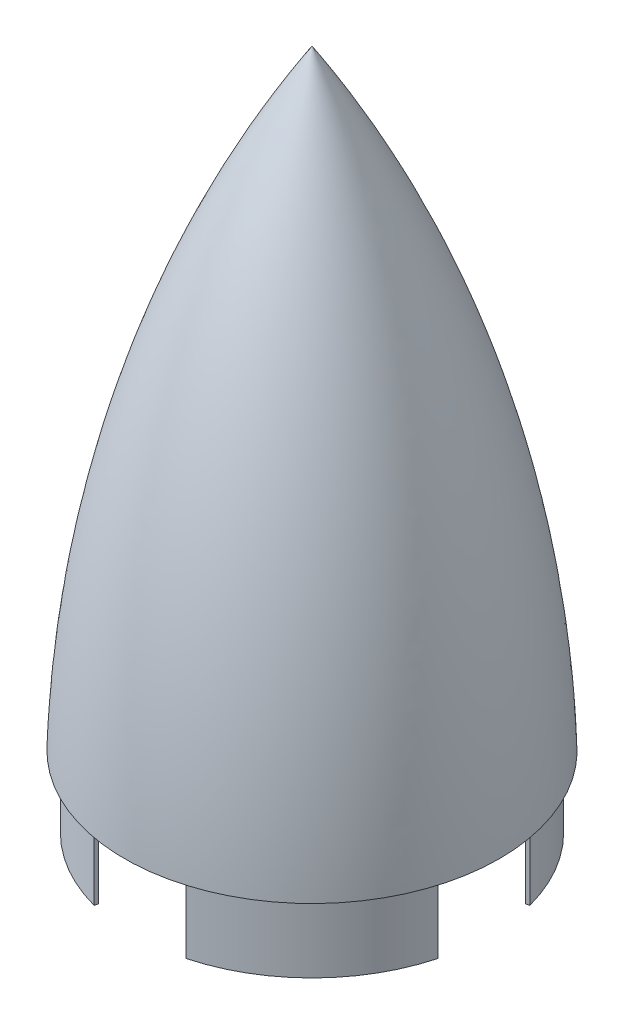
SolidWorks part; units mm, degrees
ref_plane "Front Plane" through (0, 0, 0) normal (0, 0, 1) x (1, 0, 0)
ref_plane "Top Plane" through (0, 0, 0) normal (0, 1, 0) x (1, 0, 0)
ref_plane "Right Plane" through (0, 0, 0) normal (1, 0, 0) x (0, 0, -1)
sketch "Sketch2" plane through (0, 0, 0) normal (0, 0, 1) x (1, 0, 0)
  line L0 (0, 0) -> (0, 304.8) construction
  line L1 (-93.6498, 0) -> (-88.9, 0)
  line L2 (0, 304.8) -> (0, 299.72)
  arc A0 (0, 304.8) -> (-93.6498, 0) centre (507.5687, -17.9374) ccw
  arc A1 (0, 299.72) -> (-88.9, 0) centre (553.2478, -27.4232) ccw
  dimension "D1" = 304.8
  dimension "D2" = 5.08
  dimension "D3" = 4.7498
  dimension "D4" = 88.9
revolve "Revolve1" add sketch "Sketch2" angle 360 about L2
sketch "Sketch3" plane through (0, 0, 0) normal (0, -1, 0) x (1, 0, 0)
  circle A0 centre (0, 0) radius 88.9
  circle A1 centre (0, 0) radius 86.995
  dimension "D1" = 177.8
extrude "Boss-Extrude1" add sketch "Sketch3" along normal blind 35.56
sketch "Sketch4" plane through (0, 0, 0) normal (0, -1, 0) x (1, 0, 0)
  line L0 (0, 0) -> (110.7142, 0) construction
  line L3 (0, 0) -> (85.8708, -23.009) construction
  line L4 (0, 0) -> (85.8708, 23.009) construction
  line L5 (85.8708, -23.009) -> (84.0307, -22.516)
  line L7 (84.0307, 22.516) -> (85.8708, 23.009)
  line L8 (0, 0) -> (-116.7737, 0) construction
  line L9 (0, -115.7458) -> (0, 110.8117) construction
  line L10 (0, 0) -> (-107.5717, 28.8237) construction
  line L11 (0, 0) -> (-107.9537, -28.9261) construction
  line L12 (0, 0) -> (-28.2493, -105.4278) construction
  line L13 (0, 0) -> (30.1026, -112.3444) construction
  line L14 (0, 0) -> (-30.4455, 113.624) construction
  line L15 (0, 0) -> (30.7288, 114.6813) construction
  line L16 (-22.516, 84.0307) -> (-23.009, 85.8708)
  line L17 (23.009, 85.8708) -> (22.516, 84.0307)
  line L18 (-84.0307, -22.516) -> (-85.8708, -23.009)
  line L19 (-84.0307, 22.516) -> (-85.8708, 23.009)
  line L20 (23.009, -85.8708) -> (22.516, -84.0307)
  line L21 (-22.516, -84.0307) -> (-23.009, -85.8708)
  circle A3 centre (0, 0) radius 88.9 construction
  circle A4 centre (0, 0) radius 88.9 construction
  circle A5 centre (0, 0) radius 86.995 construction
  arc A6 (85.8708, -23.009) -> (85.8708, 23.009) centre (0, 0) ccw
  arc A7 (84.0307, -22.516) -> (84.0307, 22.516) centre (0, 0) ccw
  arc A8 (23.009, -85.8708) -> (-23.009, -85.8708) centre (0, 0) cw
  arc A9 (22.516, -84.0307) -> (-22.516, -84.0307) centre (0, 0) cw
  arc A10 (-84.0307, -22.516) -> (-84.0307, 22.516) centre (0, 0) cw
  arc A11 (-85.8708, 23.009) -> (-85.8708, -23.009) centre (0, 0) ccw
  arc A12 (22.516, 84.0307) -> (-22.516, 84.0307) centre (0, 0) ccw
  arc A13 (23.009, 85.8708) -> (-23.009, 85.8708) centre (0, 0) ccw
  dimension "D3" = 88.9
  dimension "D4" = 86.995
  dimension "D1" = 15
  dimension "D2" = 15
  dimension "D5" = 30
  dimension "D6" = 15
  dimension "D7" = 15
  dimension "D8" = 30
  dimension "D9" = 30
  dimension "D10" = 15
extrude "Cut-Extrude1" cut sketch "Sketch4" along normal up to surface (35.56 mm away) up to face at (88.9, -35.56, 0)
equation "\"D4@Sketch2\"=3.5"
